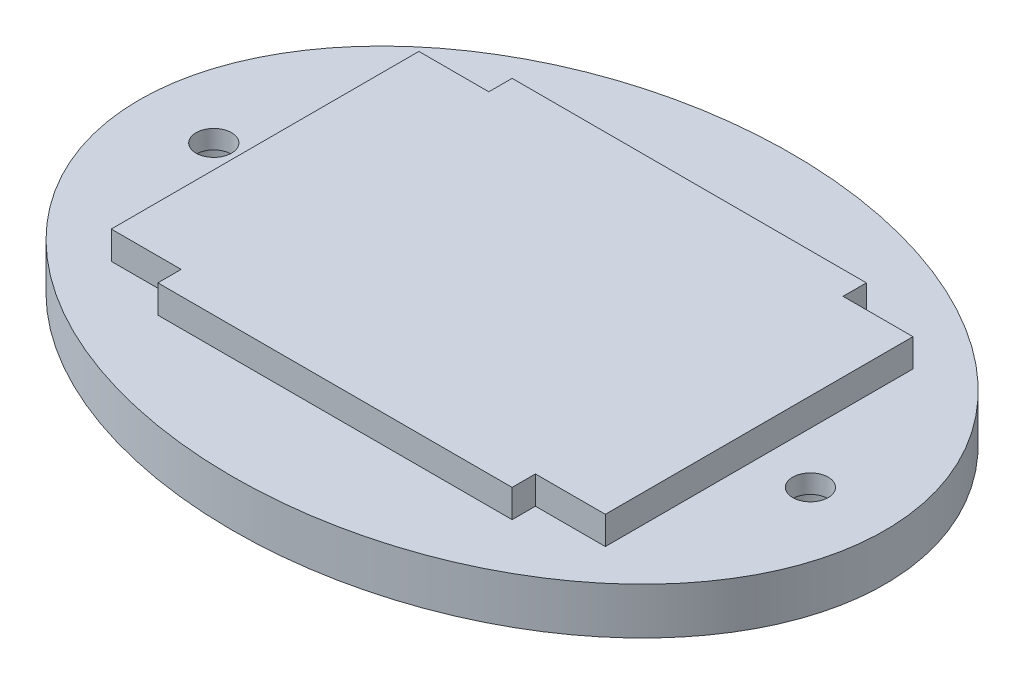
SolidWorks part; units mm, degrees
ref_plane "Front Plane" through (0, 0, 0) normal (0, 0, 1) x (1, 0, 0)
ref_plane "Top Plane" through (0, 0, 0) normal (0, 1, 0) x (1, 0, 0)
ref_plane "Right Plane" through (0, 0, 0) normal (1, 0, 0) x (0, 0, -1)
sketch "Sketch1" plane through (0, 0, 0) normal (0, 1, 0) x (1, 0, 0)
  ellipse E0 centre (0, 0) end of major axis (-40, 0) minor radius 30
  dimension "D1" = 80
  dimension "D2" = 60
extrude "Boss-Extrude1" add sketch "Sketch1" along normal blind 5
sketch "Sketch2" plane through (0, 5, 0) normal (0, 1, 0) x (1, 0, 0)
  line L0 (-19, 16.5) -> (-26.5, 16.5)
  line L1 (19, -19) -> (-19, -19)
  line L2 (19, -19) -> (19, -16.5)
  line L3 (19, 19) -> (-19, 19)
  line L4 (-19, -19) -> (-19, -16.5)
  line L5 (19, -19) -> (-19, 19) construction
  line L6 (19, 19) -> (-19, -19) construction
  line L7 (26.5, -16.5) -> (19, -16.5)
  line L8 (26.5, -16.5) -> (26.5, 16.5)
  line L9 (26.5, 16.5) -> (19, 16.5)
  line L10 (-26.5, -16.5) -> (-26.5, 16.5)
  line L11 (26.5, -16.5) -> (-26.5, 16.5) construction
  line L12 (26.5, 16.5) -> (-26.5, -16.5) construction
  line L13 (-19, 16.5) -> (-19, 19)
  line L14 (-19, -16.5) -> (-26.5, -16.5)
  line L15 (19, 16.5) -> (19, 19)
  point P0 (0, 0)
  point P6 (0, 0)
  dimension "D1" = 38
  dimension "D2" = 38
  dimension "D3" = 33
  dimension "D4" = 53
extrude "Boss-Extrude2" add sketch "Sketch2" along normal blind 3
sketch "Sketch3" plane through (0, 0, 0) normal (0, -1, 0) x (1, 0, 0)
  circle A0 centre (32, 0) radius 1.905
  circle A1 centre (-32, 0) radius 1.905
  point P4 (0, 0)
  point P5 (30, 0)
  point P6 (0, 0)
  dimension "D1" = 3.81
  dimension "D2" = 3.81
  dimension "D3" = 32
  dimension "D4" = 32
extrude "Cut-Extrude1" cut sketch "Sketch3" against normal blind 10
sketch "Sketch4" plane through (0, 0, 0) normal (0, -1, 0) x (1, 0, 0)
  circle A2 centre (-32, 0) radius 3.405
  circle A3 centre (-32, 0) radius 3.405
  circle A5 centre (32, 0) radius 3.405
  circle A6 centre (32, 0) radius 3.405
  dimension "D1" = 1.5
  dimension "D2" = 1.5
extrude "Cut-Extrude2" cut sketch "Sketch4" against normal blind 3
